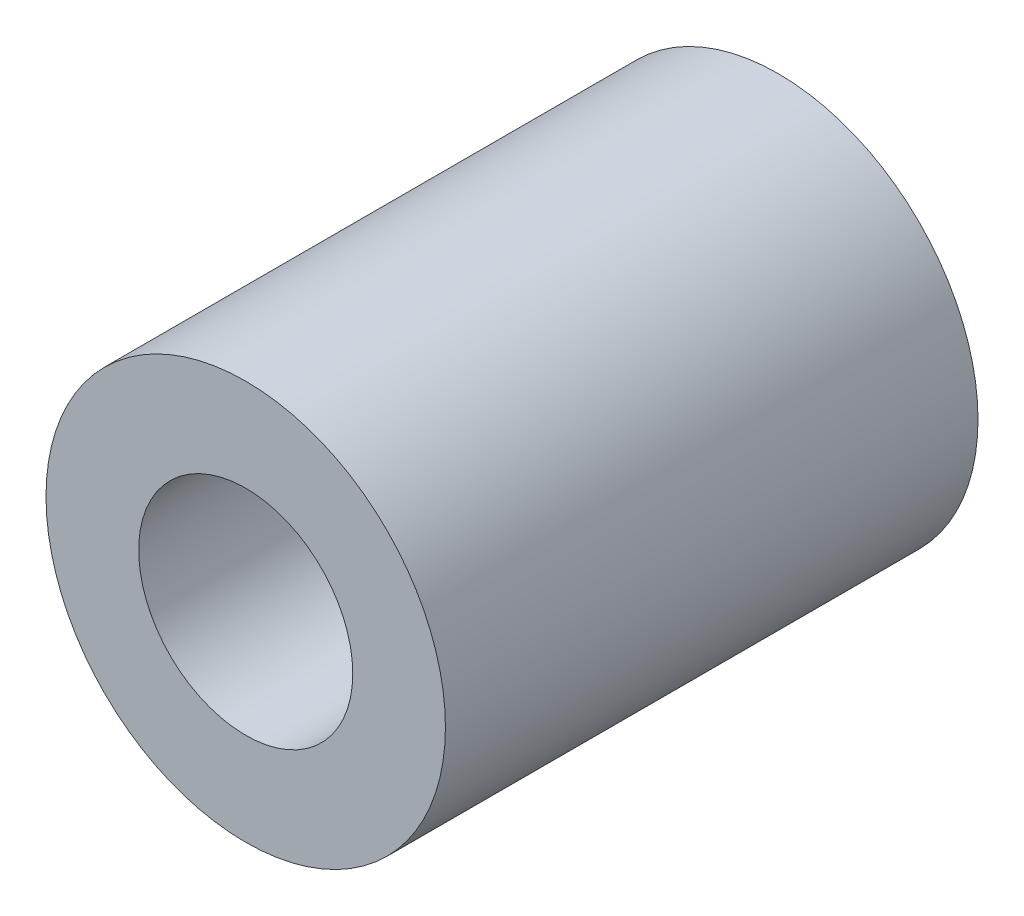
SolidWorks part; units mm, degrees
material "6061 Alloy"
ref_plane "Front Plane" through (0, 0, 0) normal (0, 0, 1) x (1, 0, 0)
ref_plane "Top Plane" through (0, 0, 0) normal (0, 1, 0) x (1, 0, 0)
ref_plane "Right Plane" through (0, 0, 0) normal (1, 0, 0) x (0, 0, -1)
sketch "Sketch1" plane through (0, 0, 0) normal (0, 0, 1) x (1, 0, 0)
  circle A0 centre (0, 0) radius 2.5527
  circle A1 centre (0, 0) radius 4.7625
  dimension "D1" = 5.1054
  dimension "D2" = 9.525
extrude "Boss-Extrude1" add sketch "Sketch1" along normal blind 12.7
